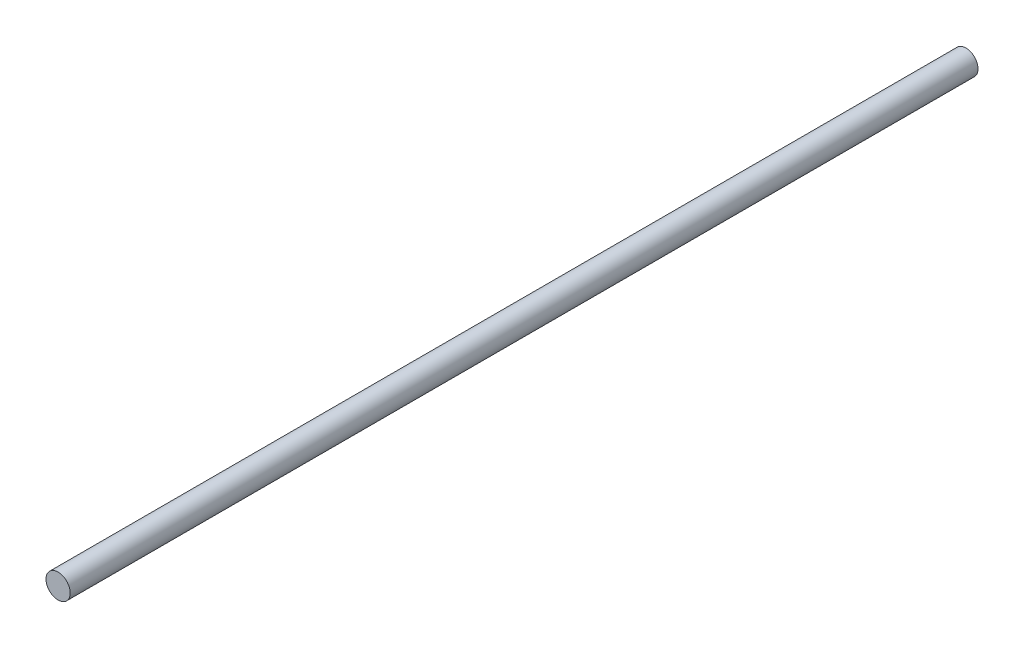
SolidWorks part; units mm, degrees
material "1023 Chapa de acero al carbono (SS)"
ref_plane "Alzado" through (0, 0, 0) normal (0, 0, 1) x (1, 0, 0)
ref_plane "Planta" through (0, 0, 0) normal (0, 1, 0) x (1, 0, 0)
ref_plane "Vista lateral" through (0, 0, 0) normal (1, 0, 0) x (0, 0, -1)
sketch "Croquis1" plane through (0, 0, 0) normal (0, 0, 1) x (1, 0, 0)
  circle A0 centre (0, 0) radius 1
  dimension "D1" = 2
extrude "Saliente-Extruir1" add sketch "Croquis1" along normal blind 75
